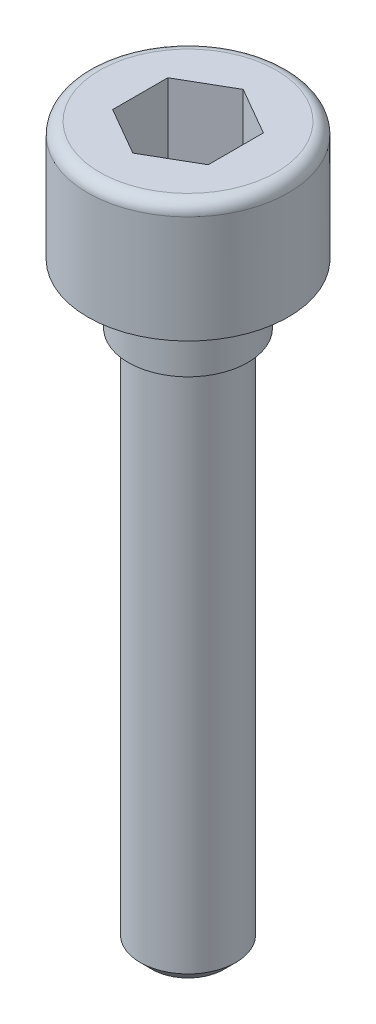
SolidWorks part; units mm, degrees
material "acero"
ref_plane "Alzado" through (0, 0, 0) normal (0, 0, 1) x (1, 0, 0)
ref_plane "Planta" through (0, 0, 0) normal (0, 1, 0) x (1, 0, 0)
ref_plane "Vista lateral" through (0, 0, 0) normal (1, 0, 0) x (0, 0, -1)
sketch "Croquis1" plane through (0, 0, 0) normal (0, 0, 1) x (1, 0, 0)
  line L0 (0, 0) -> (0, -60.9498) construction
  line L1 (0, 0) -> (4.2, 0)
  line L2 (4.2, 0) -> (4.2, -5)
  line L3 (4.2, -5) -> (2.5, -5)
  line L4 (2.5, -5) -> (2.5, -30)
  line L5 (2.5, -30) -> (0, -30)
  line L6 (0, -30) -> (0, 0)
  dimension "D1" = 25
  dimension "D2" = 5
  dimension "D3" = 8.4
  dimension "D4" = 5
revolve "Revolución1" add sketch "Croquis1" angle 360 about L0
cosmetic thread "Rosca cosmética1" parameters "D2"=4.11
sketch "Croquis2" plane through (0, 0, 0) normal (0, 1, 0) x (1, 0, 0)
  line L1 (2, 1.1547) -> (0, 2.3094)
  line L2 (0, 2.3094) -> (-2, 1.1547)
  line L3 (-2, 1.1547) -> (-2, -1.1547)
  line L4 (-2, -1.1547) -> (0, -2.3094)
  line L5 (0, -2.3094) -> (2, -1.1547)
  line L6 (2, -1.1547) -> (2, 1.1547)
  circle A0 centre (0, 0) radius 2 construction
  dimension "D1" = 4
extrude "Cortar-Extruir1" cut sketch "Croquis2" against normal blind 3
chamfer "Chaflán1" distance 0.5 angle 45 1 edges at (0, -30, 2.5)
fillet "Redondeo1" radius 0.5 1 edges at (0, 0, 4.2)
sketch "Croquis3" plane through (0, 0, 0) normal (0, 0, 1) x (1, 0, 0)
  line L0 (0, 0) -> (0, -33.6208) construction
  line L1 (2, -7.5) -> (2.5, -7.5)
  line L2 (2, -7.5) -> (2, -30)
  line L3 (2, -30) -> (2.5, -30)
  line L4 (2.5, -7.5) -> (2.5, -30)
  line L5 (-4.2, -5) -> (4.2, -5) construction
  line L6 (-2, -30) -> (2, -30) construction
  line L7 (2.5, -29.5) -> (2.5, -5) construction
  dimension "D1" = 4
  dimension "D2" = 2.5
revolve "Cortar-Revolución1" cut sketch "Croquis3" angle 360 about L0
chamfer "Chaflán2" distance 0.5 angle 45 1 edges at (0, -30, 2)
